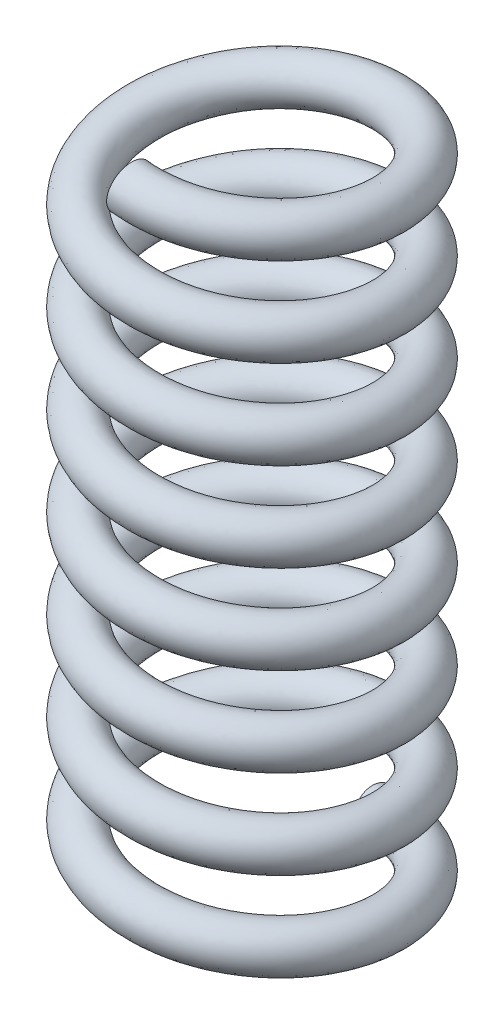
SolidWorks part; units mm, degrees
ref_plane "Front Plane" through (0, 0, 0) normal (0, 0, 1) x (1, 0, 0)
ref_plane "Top Plane" through (0, 0, 0) normal (0, 1, 0) x (1, 0, 0)
ref_plane "Right Plane" through (0, 0, 0) normal (1, 0, 0) x (0, 0, -1)
sketch "Sketch2" plane through (0, 0, 0) normal (0, 1, 0) x (1, 0, 0)
  circle A0 centre (0, 0) radius 2.75
  dimension "D1" = 5.5
curve "Helix/Spiral1" pitch 2 height 15 turns 7.5
ref_plane "Plane1" through (0, 0, -2.75) normal (0.9934, 0.115, 0) x (-0.0261, 0.2255, 0.9739)
sketch "Sketch4" plane through (0, 0, -2.75) normal (0.9934, 0.115, 0) x (-0.0261, 0.2255, 0.9739)
  circle A0 centre (-0.0247, 0) radius 0.5
sweep "Sweep1" add profiles "Sketch4" path "Helix/Spiral1"
ref_plane "Plane3" through (0, 15.5, 0) normal (0, 1, 0) x (1, 0, 0)
ref_plane "Plane4" through (0, 0, 0) normal (0, 1, 0) x (1, 0, 0)
sketch "Sketch5" plane through (0, 0, 0) normal (0, 1, 0) x (1, 0, 0)
  circle A0 centre (0, 0) radius 3.2339
